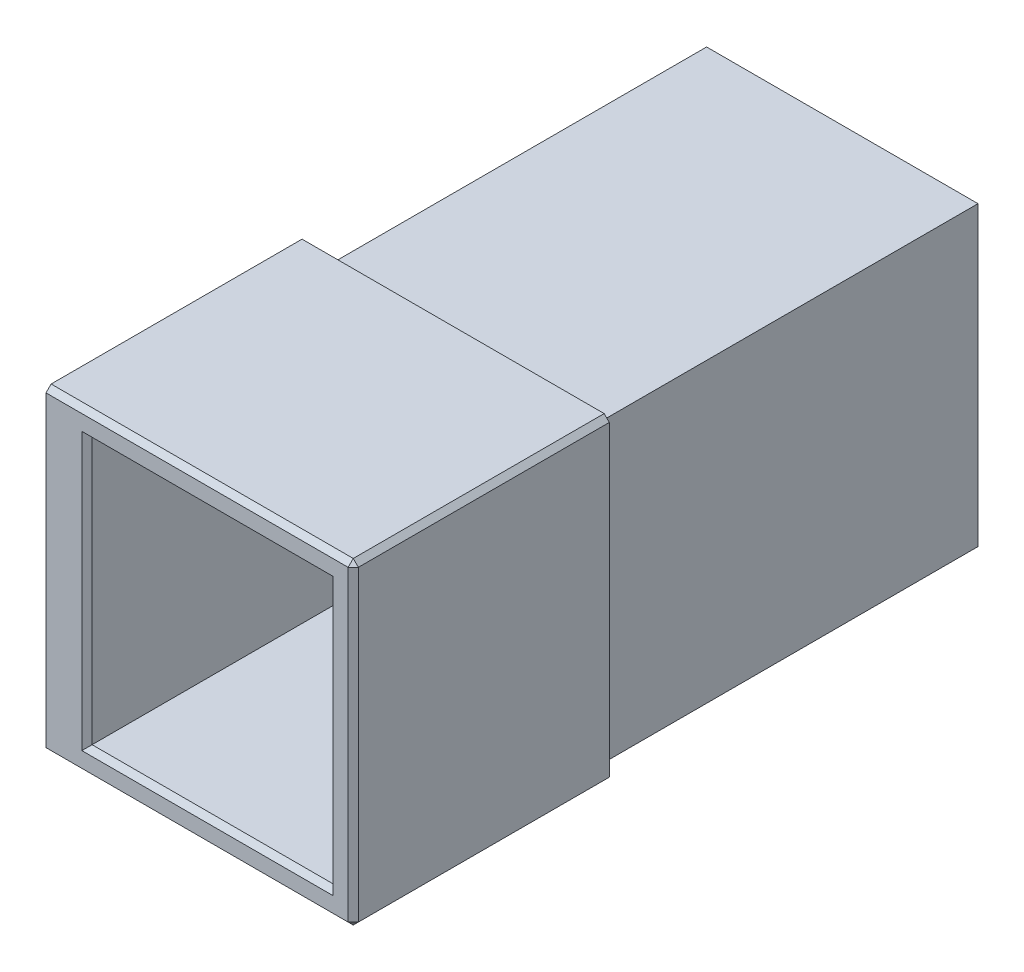
SolidWorks part; units mm, degrees
material "Petg 30% Infill"
ref_plane "Front Plane" through (0, 0, 0) normal (0, 0, 1) x (1, 0, 0)
ref_plane "Top Plane" through (0, 0, 0) normal (0, 1, 0) x (1, 0, 0)
ref_plane "Right Plane" through (0, 0, 0) normal (1, 0, 0) x (0, 0, -1)
sketch "Sketch1" plane through (0, 0, 0) normal (0, 0, 1) x (1, 0, 0)
  line L0 (17.5408, -97.5447) -> (17.5408, -113.5447)
  line L5 (64.5408, -92.5447) -> (17.5408, -92.5447)
  line L6 (64.5408, -92.5447) -> (64.5408, -40.5447)
  line L7 (64.5408, -40.5447) -> (17.5408, -40.5447)
  line L8 (17.5408, -92.5447) -> (17.5408, -40.5447)
  line L9 (64.5408, -92.5447) -> (17.5408, -40.5447) construction
  line L10 (64.5408, -40.5447) -> (17.5408, -92.5447) construction
  line L11 (69.5408, -97.5447) -> (17.5408, -97.5447)
  line L12 (69.5408, -97.5447) -> (69.5408, -35.5447)
  line L13 (69.5408, -35.5447) -> (9.5408, -35.5447)
  line L14 (9.5408, -113.5447) -> (9.5408, -35.5447)
  line L17 (17.5408, -113.5447) -> (9.5408, -113.5447)
  point P5 (41.0408, -66.5447)
  point P10 (41.0408, -66.5447)
  dimension "D1" = 8
  dimension "D2" = 47
  dimension "D3" = 52
  dimension "D5" = 78
  dimension "D6" = 5
  dimension "D4" = 5
  dimension "D7" = 5
extrude "Boss-Extrude1" add sketch "Sketch1" along normal blind 50
sketch "Sketch8" plane through (17.5408, 0, 0) normal (1, 0, 0) x (0, 0, -1)
  line L0 (-50, -97.5447) -> (0, -97.5447) construction
  line L1 (-50, -113.5447) -> (-25, -113.5447)
  line L2 (-50, -113.5447) -> (-50, -97.5447)
  line L3 (-50, -97.5447) -> (-25, -97.5447)
  line L4 (-25, -113.5447) -> (-25, -97.5447)
extrude "Cut-Extrude1" cut sketch "Sketch8" against normal blind 10
sketch "Sketch9" plane through (9.5408, 0, 0) normal (-1, 0, 0) x (0, 0, 1)
  line L0 (35, -46.0447) -> (28, -46.0447) construction
  line L1 (35, -49.7947) -> (28, -49.7947)
  line L2 (35, -42.2947) -> (28, -42.2947)
  line L3 (15, -103.0447) -> (8, -103.0447) construction
  line L4 (15, -106.7947) -> (8, -106.7947)
  line L5 (15, -99.2947) -> (8, -99.2947)
  line L6 (25, -113.5447) -> (25, -97.5447) construction
  line L7 (0, -74.5447) -> (21.5, -74.5447) construction
  line L8 (0, -35.5447) -> (0, -113.5447) construction
  line L9 (31.5, -46.0447) -> (11.5, -103.0447) construction
  arc A0 (35, -49.7947) -> (35, -42.2947) centre (35, -46.0447) ccw
  arc A1 (28, -42.2947) -> (28, -49.7947) centre (28, -46.0447) ccw
  arc A2 (15, -106.7947) -> (15, -99.2947) centre (15, -103.0447) ccw
  arc A3 (8, -99.2947) -> (8, -106.7947) centre (8, -103.0447) ccw
  point P2 (31.5, -46.0447)
  point P7 (11.5, -103.0447)
  point P22 (21.5, -74.5447)
  dimension "D1" = 7.5
  dimension "D2" = 10
  dimension "D3" = 10
  dimension "D4" = 7
  dimension "D5" = 57
extrude "Cut-Extrude2" cut sketch "Sketch9" against normal blind 3.5 from offset 2 offset against normal yes
sketch "Sketch10" plane through (9.5408, 0, 0) normal (-1, 0, 0) x (0, 0, 1)
  line L0 (35, -46.0447) -> (28, -46.0447) construction
  line L1 (35, -48.0947) -> (32.4788, -48.0947)
  line L2 (35, -43.9947) -> (32.4788, -43.9947)
  line L3 (8, -103.0447) -> (15, -103.0447) construction
  line L4 (12.4788, -100.9947) -> (15, -100.9947)
  line L5 (12.4788, -105.0947) -> (15, -105.0947)
  arc A0 (30.4882, -43.2391) -> (30.4882, -48.8502) centre (28, -46.0447) ccw
  arc A1 (10.4882, -100.2391) -> (10.4882, -105.8502) centre (8, -103.0447) ccw
  arc A2 (35, -48.0947) -> (35, -43.9947) centre (35, -46.0447) ccw
  arc A5 (15, -105.0947) -> (15, -100.9947) centre (15, -103.0447) ccw
  arc A6 (8, -99.2947) -> (8, -106.7947) centre (8, -103.0447) ccw construction
  arc A7 (15, -106.7947) -> (15, -99.2947) centre (15, -103.0447) ccw construction
  arc A8 (28, -42.2947) -> (28, -49.7947) centre (28, -46.0447) ccw construction
  arc A9 (35, -49.7947) -> (35, -42.2947) centre (35, -46.0447) ccw construction
  arc A10 (30.4882, -43.2391) -> (32.4788, -43.9947) centre (32.4788, -40.9947) ccw
  arc A11 (32.4788, -48.0947) -> (30.4882, -48.8502) centre (32.4788, -51.0947) ccw
  arc A12 (10.4882, -100.2391) -> (12.4788, -100.9947) centre (12.4788, -97.9947) ccw
  arc A13 (12.4788, -105.0947) -> (10.4882, -105.8502) centre (12.4788, -108.0947) ccw
  point P5 (31.9062, -46.5675)
  point P10 (11.5, -103.0447)
  dimension "D3" = 3
  dimension "D1" = 4.1
  dimension "D2" = 4.1
extrude "Cut-Extrude3" cut sketch "Sketch10" against normal blind 3.5
chamfer "Chamfer1" distance 1 angle 45 13 edges at (17.5408, -66.5447, 50) (41.0408, -92.5447, 50) (41.0408, -40.5447, 50) (64.5408, -66.5447, 50) (17.5408, -113.5447, 12.5) (39.5408, -97.5447, 50) (39.5408, -35.5447, 50) (69.5408, -97.5447, 25) (69.5408, -66.5447, 50) (69.5408, -35.5447, 25) (17.5408, -97.5447, 12.5) (13.5408, -97.5447, 25) (17.5408, -105.5447, 25)
sketch "Sketch6" plane through (0, 0, 0) normal (0, 0, -1) x (-1, 0, 0)
  line L0 (-64.5408, -40.5447) -> (-17.5408, -40.5447) construction
  line L1 (-64.5408, -92.5447) -> (-64.5408, -40.5447) construction
  line L2 (-17.5408, -40.5447) -> (-17.5408, -92.5447) construction
  line L3 (-17.5408, -92.5447) -> (-64.5408, -92.5447) construction
  line L4 (-64.5408, -40.5447) -> (-17.5408, -40.5447)
  line L5 (-64.5408, -92.5447) -> (-64.5408, -40.5447)
  line L6 (-17.5408, -40.5447) -> (-17.5408, -92.5447)
  line L7 (-17.5408, -92.5447) -> (-64.5408, -92.5447)
  line L8 (-67.5408, -37.5447) -> (-14.5408, -37.5447)
  line L9 (-14.5408, -37.5447) -> (-14.5408, -95.5447)
  line L10 (-14.5408, -95.5447) -> (-67.5408, -95.5447)
  line L11 (-67.5408, -95.5447) -> (-67.5408, -37.5447)
  dimension "D1" = 3
extrude "Boss-Extrude3" add sketch "Sketch6" along normal blind 74
chamfer "Chamfer2" distance 1 angle 45 4 edges at (41.0408, -95.5447, 0) (14.5408, -66.5447, 0) (41.0408, -37.5447, 0) (67.5408, -66.5447, 0)
equation "\"D4@Sketch1\"=\"D6@Sketch1\""
equation "\"D7@Sketch1\"=\"D6@Sketch1\""
